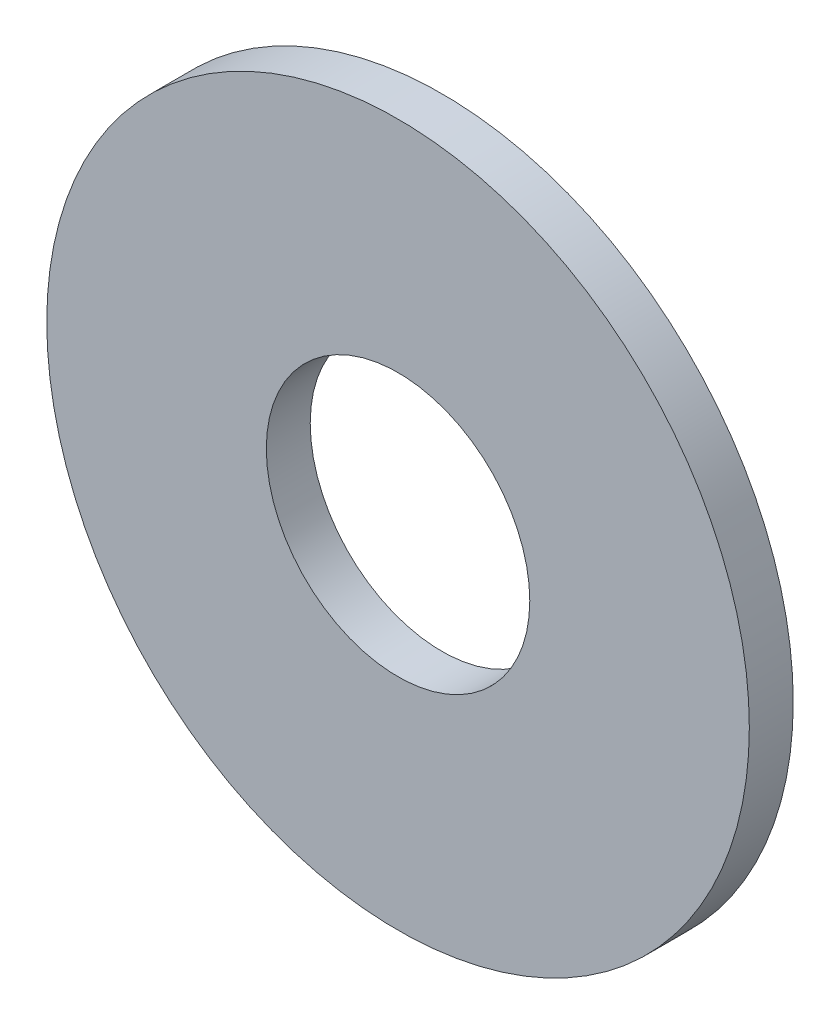
SolidWorks part; units mm, degrees
ref_plane "Front Plane" through (0, 0, 0) normal (0, 0, 1) x (1, 0, 0)
ref_plane "Top Plane" through (0, 0, 0) normal (0, 1, 0) x (1, 0, 0)
ref_plane "Right Plane" through (0, 0, 0) normal (1, 0, 0) x (0, 0, -1)
sketch "Sketch1" plane through (0, 0, 0) normal (0, 0, 1) x (1, 0, 0)
  circle A0 centre (0, 0) radius 3
  circle A1 centre (0, 0) radius 8
  dimension "D1" = 6
  dimension "D2" = 16
extrude "Boss-Extrude1" add sketch "Sketch1" along normal blind 1
